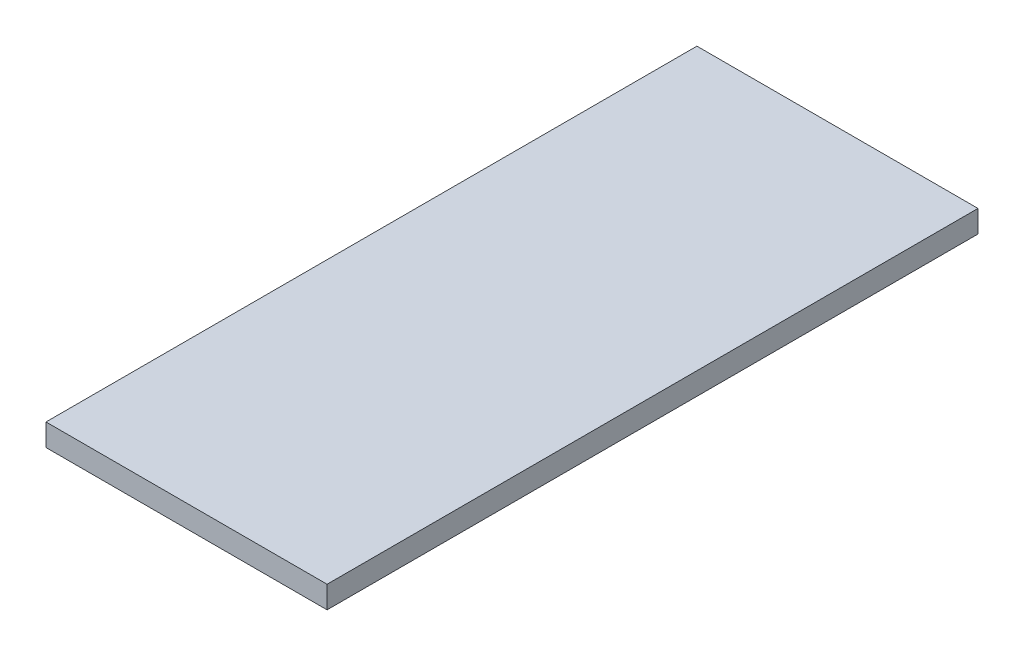
SolidWorks part; units mm, degrees
ref_plane "Front Plane" through (0, 0, 0) normal (0, 0, 1) x (1, 0, 0)
ref_plane "Top Plane" through (0, 0, 0) normal (0, 1, 0) x (1, 0, 0)
ref_plane "Right Plane" through (0, 0, 0) normal (1, 0, 0) x (0, 0, -1)
sketch "Sketch1" plane through (0, 0, 0) normal (0, 1, 0) x (1, 0, 0)
  line L1 (120.65, -279.4) -> (-120.65, -279.4)
  line L2 (120.65, -279.4) -> (120.65, 279.4)
  line L3 (120.65, 279.4) -> (-120.65, 279.4)
  line L4 (-120.65, -279.4) -> (-120.65, 279.4)
  line L5 (120.65, -279.4) -> (-120.65, 279.4) construction
  line L6 (120.65, 279.4) -> (-120.65, -279.4) construction
  point P0 (0, 0)
  dimension "D1" = 241.3
  dimension "D2" = 558.8
extrude "Boss-Extrude1" add sketch "Sketch1" along normal mid plane 19.05
